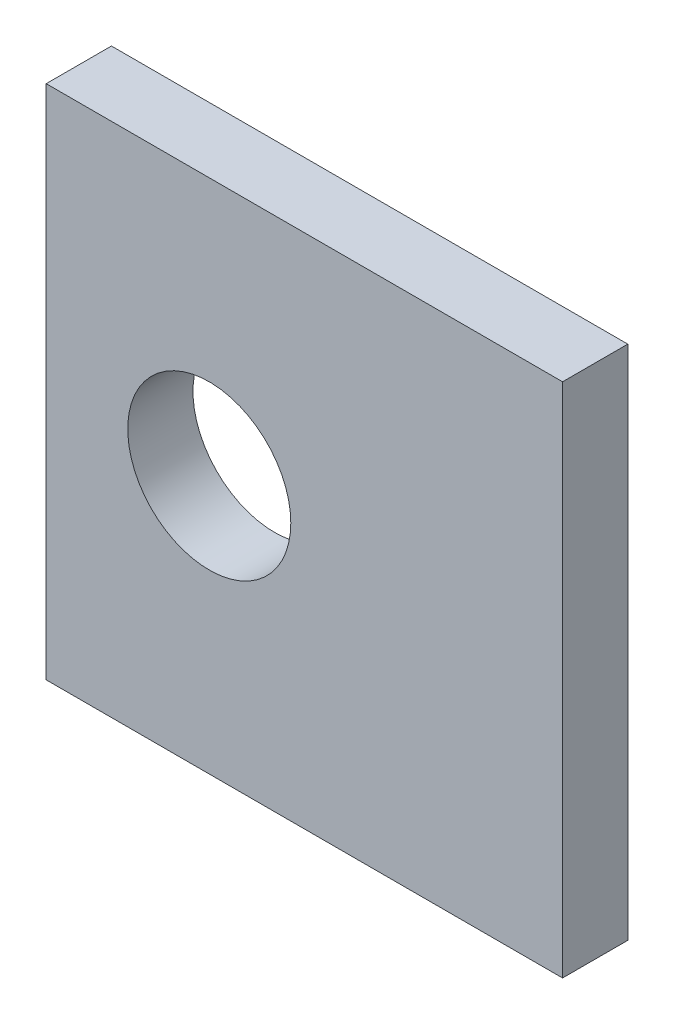
SolidWorks part; units mm, degrees
ref_plane "Front Plane" through (0, 0, 0) normal (0, 0, 1) x (1, 0, 0)
ref_plane "Top Plane" through (0, 0, 0) normal (0, 1, 0) x (1, 0, 0)
ref_plane "Right Plane" through (0, 0, 0) normal (1, 0, 0) x (0, 0, -1)
sketch "Sketch1" plane through (0, 0, 0) normal (0, 1, 0) x (1, 0, 0)
  line L1 (-19, -2.4) -> (19, -2.4)
  line L2 (-19, -2.4) -> (-19, 2.4)
  line L3 (-19, 2.4) -> (19, 2.4)
  line L4 (19, -2.4) -> (19, 2.4)
  line L5 (-19, -2.4) -> (19, 2.4) construction
  line L6 (-19, 2.4) -> (19, -2.4) construction
  point P0 (0, 0)
  dimension "D1" = 38
  dimension "D2" = 4.8
extrude "Boss-Extrude1" add sketch "Sketch1" along normal blind 38
sketch "Sketch2" plane through (0, 0, 0) normal (0, -1, 0) x (1, 0, 0)
  line L0 (19, 2.4) -> (19, -2.4) construction
  line L1 (0, 0) -> (0, 50000) construction
  line L2 (0, 0) -> (50000, 0) construction
  circle A0 centre (7.75, 0) radius 1.5 construction
  circle A1 centre (7.75, 0) radius 2
  circle A2 centre (-7.75, 0) radius 2
  point P2 (9.25, 0)
  dimension "D2" = 3
  dimension "D3" = 4
  dimension "D1" = 9.75
extrude "Cut-Extrude1" cut sketch "Sketch2" against normal blind 10
sketch "Sketch3" plane through (0, 0, 2.4) normal (0, 0, 1) x (1, 0, 0)
  line L0 (-19, 19) -> (49981, 19) construction
  line L1 (-19, 38) -> (-19, 0) construction
  circle A0 centre (-7, 19) radius 6
  point P4 (-19, 19)
  dimension "D1" = 12
  dimension "D2" = 12
extrude "Cut-Extrude2" cut sketch "Sketch3" against normal through all contours A0
